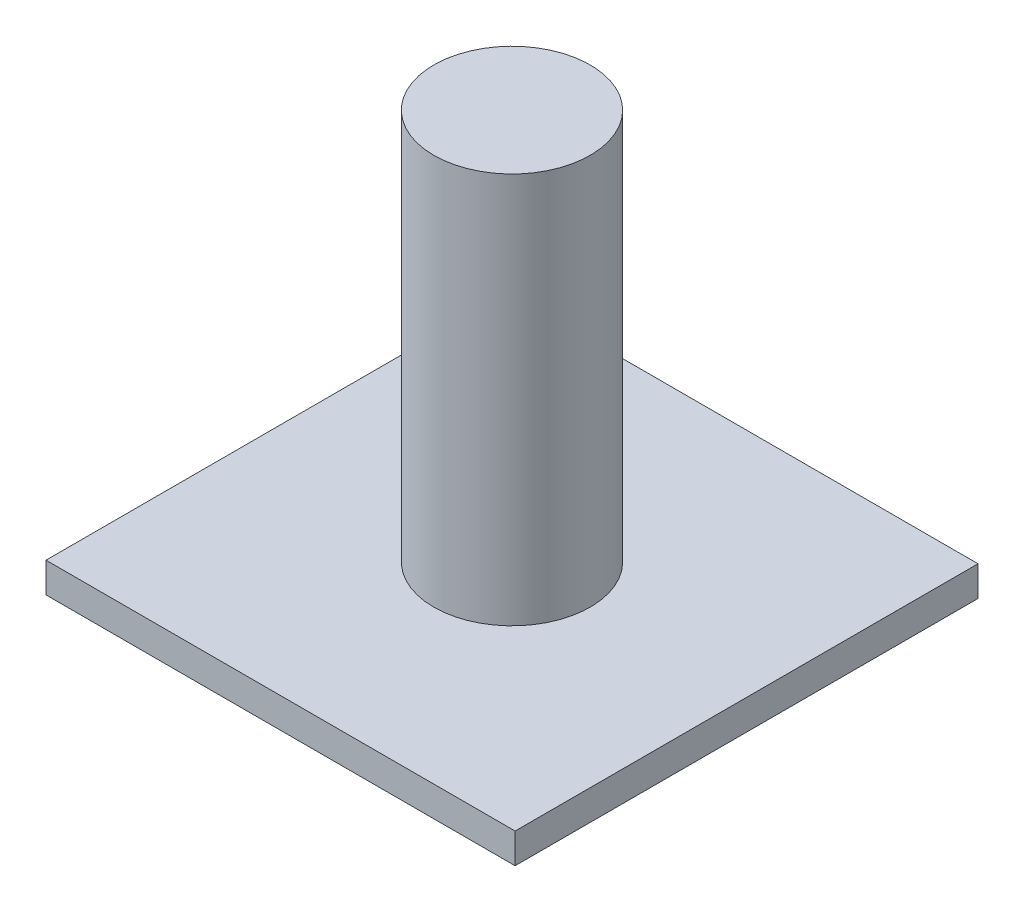
SolidWorks part; units mm, degrees
ref_plane "Front Plane" through (0, 0, 0) normal (0, 0, 1) x (1, 0, 0)
ref_plane "Top Plane" through (0, 0, 0) normal (0, 1, 0) x (1, 0, 0)
ref_plane "Right Plane" through (0, 0, 0) normal (1, 0, 0) x (0, 0, -1)
sketch "Sketch1" plane through (0, 0, 0) normal (0, 1, 0) x (1, 0, 0)
  line L1 (-38.9622, -38.4461) -> (38.9622, -38.4461)
  line L2 (-38.9622, -38.4461) -> (-38.9622, 38.4461)
  line L3 (-38.9622, 38.4461) -> (38.9622, 38.4461)
  line L4 (38.9622, -38.4461) -> (38.9622, 38.4461)
  line L5 (-38.9622, -38.4461) -> (38.9622, 38.4461) construction
  line L6 (-38.9622, 38.4461) -> (38.9622, -38.4461) construction
  point P0 (0, 0)
extrude "Boss-Extrude1" add sketch "Sketch1" along normal blind 5
sketch "Sketch2" plane through (0, 5, 0) normal (0, 1, 0) x (1, 0, 0)
  circle A0 centre (0, 0) radius 13
  dimension "D1" = 26
extrude "Boss-Extrude2" add sketch "Sketch2" along normal blind 65
